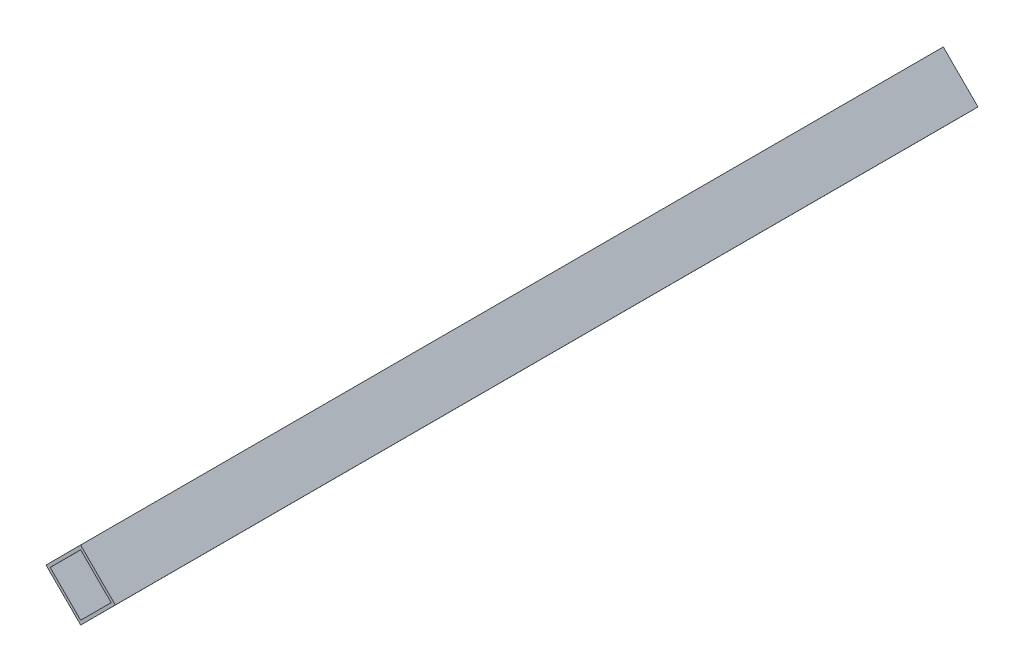
SolidWorks part; units mm, degrees
material "可鍛鑄鐵"
ref_plane "前基準面" through (0, 0, 0) normal (0, 0, 1) x (1, 0, 0)
ref_plane "上基準面" through (0, 0, 0) normal (0, 1, 0) x (1, 0, 0)
ref_plane "右基準面" through (0, 0, 0) normal (1, 0, 0) x (0, 0, -1)
sketch "草圖1" plane through (0, 0, 0) normal (0, 0, 1) x (1, 0, 0)
  line L0 (0, 0) -> (17.6938, -17.6615)
  line L1 (0, 0) -> (-17.6615, -17.6938)
  line L2 (17.6938, -17.6615) -> (0.0323, -35.3553)
  line L3 (-17.6615, -17.6938) -> (0.0323, -35.3553)
  line L4 (0.0019, -2.1213) -> (-15.5402, -17.6919)
  line L5 (0.0019, -2.1213) -> (15.5725, -17.6635)
  line L6 (-15.5402, -17.6919) -> (0.0303, -33.234)
  line L7 (15.5725, -17.6635) -> (0.0303, -33.234)
  point P0 (8.8469, -8.8308)
  dimension "D1" = 25
  dimension "D2" = 25
  dimension "D3" = 1.5
  dimension "D4" = 1.5
  dimension "D5" = 1.5
  dimension "D6" = 1.5
extrude "填料-伸長1" add sketch "草圖1" along normal blind 440
sketch "草圖2" plane through (0, 0, 0) normal (0.7065, 0.7078, 0) x (0.7078, -0.7065, 0)
  line L0 (25, -440) -> (0, -440) construction
  line L1 (25, -440) -> (25, 0) construction
  line L2 (25, 0) -> (0, 0) construction
  line L3 (0, -440) -> (0, 0) construction
  circle A0 centre (12.5, -268) radius 2.75
  circle A1 centre (12.5, -312) radius 2.75
  circle A2 centre (12.5, -128) radius 2.75
  circle A3 centre (12.5, -172) radius 2.75
  dimension "D1" = 5.5
  dimension "D2" = 5.5
  dimension "D4" = 128
  dimension "D5" = 12.5
  dimension "D6" = 12.5
  dimension "D7" = 5.5
  dimension "D8" = 5.5
  dimension "D9" = 44
  dimension "D10" = 128
  dimension "D11" = 12.5
  dimension "D3" = 44
